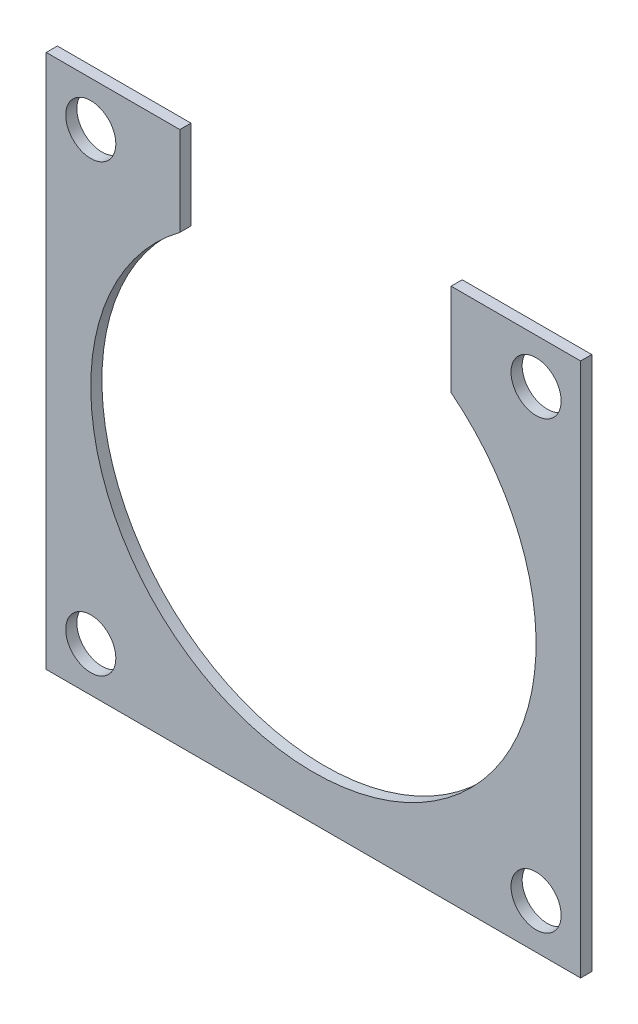
SolidWorks part; units mm, degrees
ref_plane "Front Plane" through (0, 0, 0) normal (0, 0, 1) x (1, 0, 0)
ref_plane "Top Plane" through (0, 0, 0) normal (0, 1, 0) x (1, 0, 0)
ref_plane "Right Plane" through (0, 0, 0) normal (1, 0, 0) x (0, 0, -1)
sketch "Sketch1" plane through (0, 0, 0) normal (0, 0, 1) x (1, 0, 0)
  line L1 (-38.1, 38.1) -> (38.1, 38.1)
  line L2 (-38.1, 38.1) -> (-38.1, -38.1)
  line L3 (-38.1, -38.1) -> (38.1, -38.1)
  line L4 (38.1, 38.1) -> (38.1, -38.1)
  circle A0 centre (0, 0) radius 31.75
  dimension "D5" = 63.5
  dimension "D1" = 76.2
  dimension "D2" = 76.2
  dimension "D3" = 38.1
  dimension "D4" = 38.1
extrude "Boss-Extrude1" add sketch "Sketch1" along normal blind 1.5875
sketch "Sketch2" plane through (0, 0, 1.5875) normal (0, 0, 1) x (1, 0, 0)
  line L0 (0, 25.7973) -> (0, -24.2806) construction
  line L1 (-23.5201, 0) -> (29.7887, 0) construction
  line L2 (0, 0) -> (-59.488, 59.488) construction
  circle A0 centre (-31.75, 31.75) radius 3.5725
  dimension "D1" = 45
  dimension "D2" = 31.75
  dimension "D3" = 31.75
extrude "Cut-Extrude1" cut sketch "Sketch2" against normal blind 3.175
sketch "Sketch5" plane through (0, 0, 1.5875) normal (0, 0, 1) x (1, 0, 0)
  line L0 (38.1, 38.1) -> (-38.1, 38.1) construction
  line L1 (-19.05, 64.2895) -> (19.6289, 64.2895)
  line L2 (-19.05, 64.2895) -> (-19.05, 17.78)
  line L3 (-19.05, 17.78) -> (19.6289, 17.78)
  line L4 (19.6289, 64.2895) -> (19.6289, 17.78)
  circle A0 centre (-31.75, 31.75) radius 3.5725 construction
  dimension "D1" = 20.32
  dimension "D2" = 12.7
extrude "Cut-Extrude3" cut sketch "Sketch5" against normal through all
mirror "Mirror1" about plane through (0, 0, 0) normal (1, 0, 0) of "Cut-Extrude1"
mirror "Mirror2" about plane through (0, 0, 0) normal (0, 1, 0) of "Mirror1", "Cut-Extrude1"
equation "\"D4@Sketch1\"=\"D1@Sketch1\"/2"
equation "\"D3@Sketch1\"=\"D2@Sketch1\"/2"
